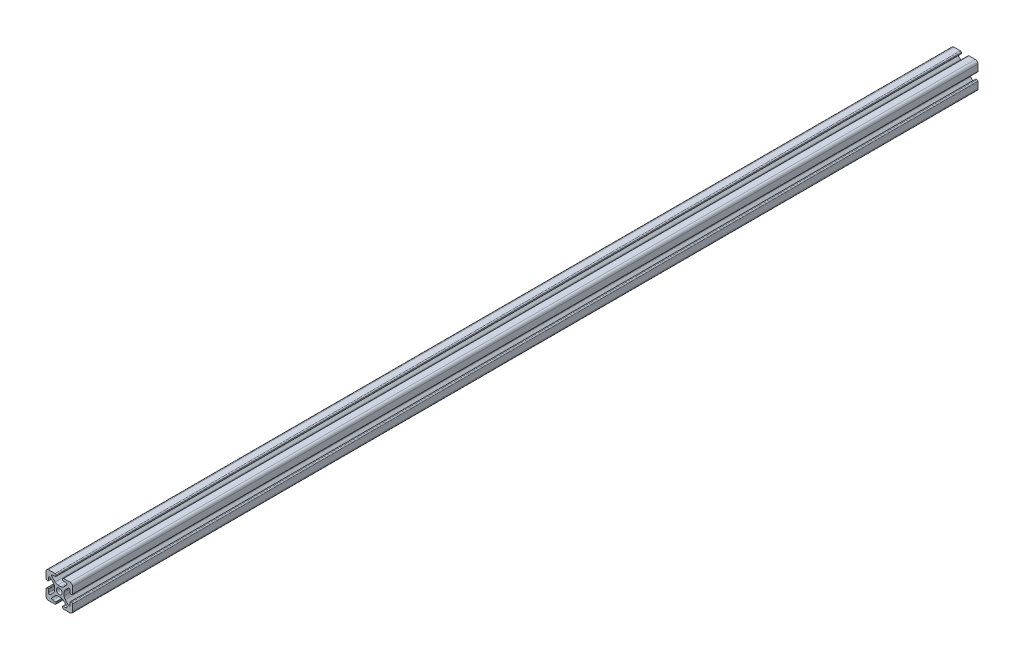
SolidWorks part; units mm, degrees
ref_plane "Front Plane" through (0, 0, 0) normal (0, 0, 1) x (1, 0, 0)
ref_plane "Top Plane" through (0, 0, 0) normal (0, 1, 0) x (1, 0, 0)
ref_plane "Right Plane" through (0, 0, 0) normal (1, 0, 0) x (0, 0, -1)
sketch "Sketch1" plane through (0, 0, 0) normal (0, 0, 1) x (1, 0, 0)
  line L0 (0, 10) -> (0, -10) construction
  line L1 (10, 0) -> (-10, 0) construction
  line L2 (-2.5, 10) -> (2.5, 10) construction
  line L3 (-5.75, 8.2) -> (5.75, 8.2) construction
  circle A0 centre (0, 0) radius 2.15 construction
  point P4 (0, 0)
  point P8 (0, 0)
  point P10 (0, 3.6)
  point P14 (0, 10)
  point P17 (0, 8.2)
  dimension "Thru Hole" = 4.3
  dimension "Height" = 20
  dimension "T Slot Depth" = 6.4
  dimension "T Slot Top Width" = 5
  dimension "T Slot Max Width" = 11.5
  dimension "Wall" = 1.8
sketch "Sketch2" plane through (0, 0, 0) normal (1, 0, 0) x (0, 0, -1)
  line L0 (152.4, 0) -> (-152.4, 0) construction
  point P4 (0, 0)
  dimension "D1" = 304.8
sketch "Sketch3" plane through (0, 0, 0) normal (0, 0, 1) x (1, 0, 0)
  line L0 (3.2874, 10) -> (8, 10)
  line L1 (10, 8) -> (10, -8) construction
  line L2 (8, -10) -> (-8, -10) construction
  line L3 (-10, 10) -> (10, -10) construction
  line L4 (2.5, 9.2126) -> (2.5, 8.5048)
  line L5 (-5.75, 8.2) -> (5.75, 8.2) construction
  line L6 (2.8048, 8.2) -> (4.9118, 8.2)
  line L7 (5.5045, 6.7691) -> (3.2141, 4.4787)
  line L8 (1.0928, 3.6) -> (-1.0928, 3.6)
  line L9 (0, 10) -> (0, -10) construction
  line L10 (5.75, 8.2) -> (5.75, 0) construction
  line L11 (10, 0) -> (-10, 0) construction
  line L12 (0, 0) -> (0, 10) construction
  line L13 (-2.5, 9.2126) -> (-2.5, 8.5048)
  line L14 (-5.5045, 6.7691) -> (-3.2141, 4.4787)
  line L15 (-2.8048, 8.2) -> (-4.9118, 8.2)
  line L16 (-3.2874, 10) -> (-8, 10)
  line L17 (0, 0) -> (-10, 0) construction
  line L18 (-10, 3.2874) -> (-10, 8)
  line L19 (-8.2, 2.8048) -> (-8.2, 4.9118)
  line L20 (-6.7691, 5.5045) -> (-4.4787, 3.2141)
  line L21 (-9.2126, 2.5) -> (-8.5048, 2.5)
  line L22 (-3.6, -1.0928) -> (-3.6, 1.0928)
  line L23 (-6.7691, -5.5045) -> (-4.4787, -3.2141)
  line L24 (-8.2, -2.8048) -> (-8.2, -4.9118)
  line L25 (-9.2126, -2.5) -> (-8.5048, -2.5)
  line L26 (-10, -3.2874) -> (-10, -8)
  line L27 (9.2126, -2.5) -> (8.5048, -2.5)
  line L28 (8.2, -2.8048) -> (8.2, -4.9118)
  line L29 (6.7691, -5.5045) -> (4.4787, -3.2141)
  line L30 (3.6, -1.0928) -> (3.6, 1.0928)
  line L31 (9.2126, 2.5) -> (8.5048, 2.5)
  line L32 (6.7691, 5.5045) -> (4.4787, 3.2141)
  line L33 (8.2, 2.8048) -> (8.2, 4.9118)
  line L34 (10, 8) -> (10, 3.2874)
  line L35 (10, -3.2874) -> (10, -8)
  line L36 (3.2874, -10) -> (8, -10)
  line L37 (-3.2874, -10) -> (-8, -10)
  line L38 (-6.7691, -5.5045) -> (-4.4787, -3.2141)
  line L39 (-2.8048, -8.2) -> (-4.9118, -8.2)
  line L40 (-5.5045, -6.7691) -> (-3.2141, -4.4787)
  line L41 (-2.5, -9.2126) -> (-2.5, -8.5048)
  line L42 (1.0928, -3.6) -> (-1.0928, -3.6)
  line L43 (5.5045, -6.7691) -> (3.2141, -4.4787)
  line L44 (2.8048, -8.2) -> (4.9118, -8.2)
  line L45 (2.5, -9.2126) -> (2.5, -8.5048)
  arc A0 (4.9118, 8.2) -> (5.5045, 6.7691) centre (4.9118, 7.3618) cw
  arc A1 (3.2141, 4.4787) -> (1.0928, 3.6) centre (1.0928, 6.6) cw
  circle A2 centre (0, 0) radius 2.15 construction
  circle A3 centre (0, 0) radius 2.15
  arc A4 (3.2874, 10) -> (2.5, 9.2126) centre (3.2874, 9.2126) ccw
  arc A5 (2.5, 8.5048) -> (2.8048, 8.2) centre (2.8048, 8.5048) ccw
  arc A6 (-3.2874, 10) -> (-2.5, 9.2126) centre (-3.2874, 9.2126) cw
  arc A7 (-4.9118, 8.2) -> (-5.5045, 6.7691) centre (-4.9118, 7.3618) ccw
  arc A8 (-3.2141, 4.4787) -> (-1.0928, 3.6) centre (-1.0928, 6.6) ccw
  arc A9 (-2.5, 8.5048) -> (-2.8048, 8.2) centre (-2.8048, 8.5048) cw
  arc A10 (-8.5048, 2.5) -> (-8.2, 2.8048) centre (-8.5048, 2.8048) ccw
  arc A11 (-4.4787, 3.2141) -> (-3.6, 1.0928) centre (-6.6, 1.0928) cw
  arc A12 (-8.2, 4.9118) -> (-6.7691, 5.5045) centre (-7.3618, 4.9118) cw
  arc A13 (-10, 3.2874) -> (-9.2126, 2.5) centre (-9.2126, 3.2874) ccw
  arc A14 (-8.5048, -2.5) -> (-8.2, -2.8048) centre (-8.5048, -2.8048) cw
  arc A15 (-10, -3.2874) -> (-9.2126, -2.5) centre (-9.2126, -3.2874) cw
  arc A16 (-4.4787, -3.2141) -> (-3.6, -1.0928) centre (-6.6, -1.0928) ccw
  arc A17 (-8.2, -4.9118) -> (-6.7691, -5.5045) centre (-7.3618, -4.9118) ccw
  arc A26 (-8, -10) -> (-10, -8) centre (-8, -8) cw
  arc A27 (-8, 10) -> (-10, 8) centre (-8, 8) ccw
  arc A28 (8, 10) -> (10, 8) centre (8, 8) cw
  arc A29 (10, -8) -> (8, -10) centre (8, -8) cw
  arc A30 (8.2, -4.9118) -> (6.7691, -5.5045) centre (7.3618, -4.9118) cw
  arc A31 (4.4787, -3.2141) -> (3.6, -1.0928) centre (6.6, -1.0928) cw
  arc A32 (10, -3.2874) -> (9.2126, -2.5) centre (9.2126, -3.2874) ccw
  arc A33 (8.5048, -2.5) -> (8.2, -2.8048) centre (8.5048, -2.8048) ccw
  arc A34 (10, 3.2874) -> (9.2126, 2.5) centre (9.2126, 3.2874) cw
  arc A35 (8.2, 4.9118) -> (6.7691, 5.5045) centre (7.3618, 4.9118) ccw
  arc A36 (4.4787, 3.2141) -> (3.6, 1.0928) centre (6.6, 1.0928) ccw
  arc A37 (8.5048, 2.5) -> (8.2, 2.8048) centre (8.5048, 2.8048) cw
  arc A38 (-2.5, -8.5048) -> (-2.8048, -8.2) centre (-2.8048, -8.5048) ccw
  arc A39 (-3.2141, -4.4787) -> (-1.0928, -3.6) centre (-1.0928, -6.6) cw
  arc A40 (-4.9118, -8.2) -> (-5.5045, -6.7691) centre (-4.9118, -7.3618) cw
  arc A41 (-3.2874, -10) -> (-2.5, -9.2126) centre (-3.2874, -9.2126) ccw
  arc A42 (2.5, -8.5048) -> (2.8048, -8.2) centre (2.8048, -8.5048) cw
  arc A43 (3.2874, -10) -> (2.5, -9.2126) centre (3.2874, -9.2126) cw
  arc A44 (3.2141, -4.4787) -> (1.0928, -3.6) centre (1.0928, -6.6) ccw
  arc A45 (4.9118, -8.2) -> (5.5045, -6.7691) centre (4.9118, -7.3618) ccw
  point P36 (2.5, 10)
  point P39 (2.5, 8.2)
  point P49 (0, 3.6)
  point P77 (-3.6, 0)
  point P78 (-8.2, -2.5)
  point P79 (-10, -2.5)
  point P104 (-10, -10)
  point P110 (10, 10)
  point P114 (10, -2.5)
  point P115 (8.2, -2.5)
  point P116 (3.6, 0)
  point P141 (0, -3.6)
  dimension "D1" = 3
  dimension "D2" = 0.8382
  dimension "D4" = 0.7874
  dimension "D5" = 0.3048
  dimension "D6" = 2
  dimension "D3" = 45
extrude "Boss-Extrude1" add sketch "Sketch3" along normal blind 680 contours A45 L44 A42 L45 A43 L36 A29 L35 A32 L27 A33 L28 A30 L29 A31 L30 A36 L32 A35 L33 A37 L31 A34 L34 A28 L0 A4 L4 A5 L6 A0 L7 A1 L8 A8 L14 A7 L15 A9 L13 A6 L16 A27 L18 A13 L21 A10 L19 A12 L20 A11
